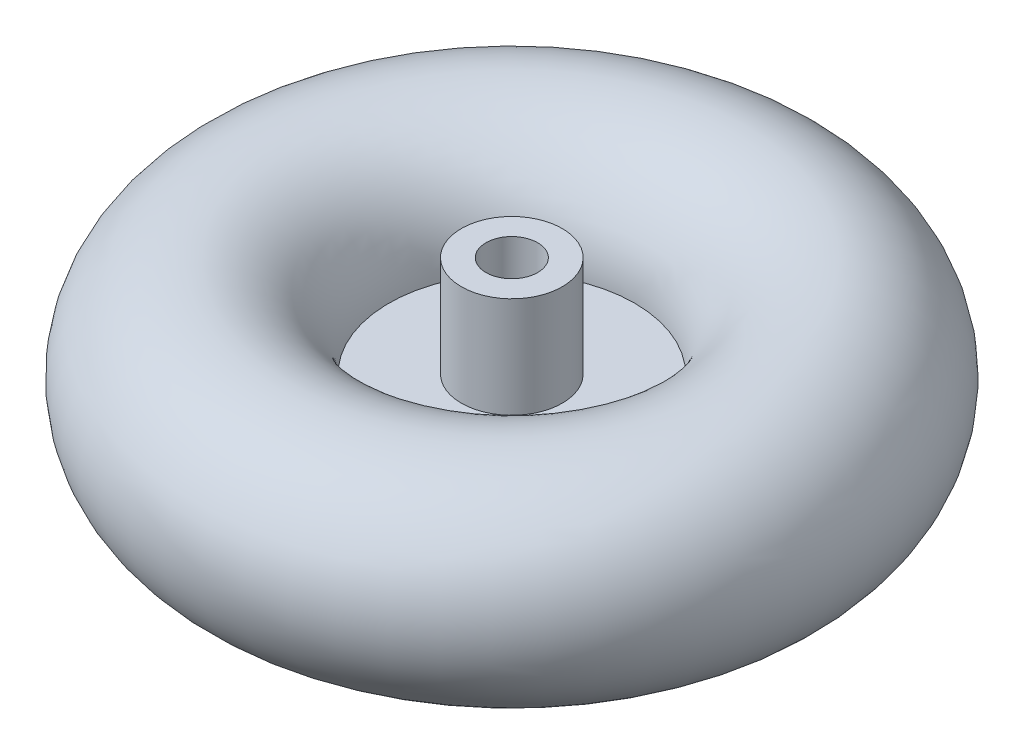
SolidWorks part; units mm, degrees
ref_plane "Спереди" through (0, 0, 0) normal (0, 0, 1) x (1, 0, 0)
ref_plane "Сверху" through (0, 0, 0) normal (0, 1, 0) x (1, 0, 0)
ref_plane "Справа" through (0, 0, 0) normal (1, 0, 0) x (0, 0, -1)
sketch "Sketch1" plane through (0, 0, 0) normal (0, 0, 1) x (1, 0, 0)
  line L0 (0, -1000) -> (0, 49000) construction
  circle A0 centre (87.5, 0) radius 40
  dimension "D1" = 80
  dimension "D2" = 87.5
revolve "Revolve1" add sketch "Sketch1" angle 360 about L0
sketch "Sketch3" plane through (0, 0, 0) normal (0, 1, 0) x (1, 0, 0)
  circle A0 centre (0, 0) radius 82.3546
extrude "Boss-Extrude1" add sketch "Sketch3" along normal mid plane 2
sketch "Sketch4" plane through (0, 1, 0) normal (0, 1, 0) x (1, 0, 0)
  circle A0 centre (0, 0) radius 19.5
  circle A1 centre (0, 0) radius 10
  dimension "D1" = 39
  dimension "D2" = 20
extrude "Boss-Extrude2" add sketch "Sketch4" along normal blind 39
sketch "Sketch5" plane through (0, 1, 0) normal (0, 1, 0) x (1, 0, 0)
  circle A0 centre (0, 0) radius 10
extrude "Cut-Extrude1" cut sketch "Sketch5" against normal through all
